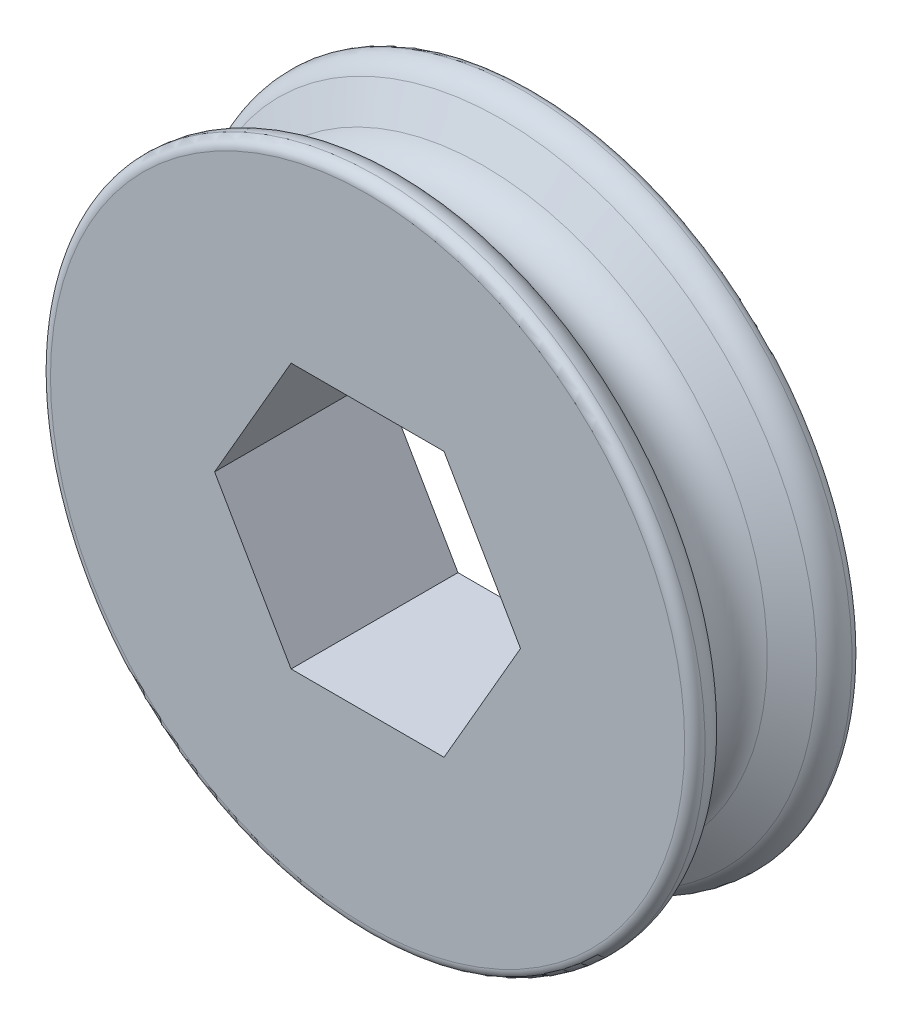
SolidWorks part; units mm, degrees
ref_plane "Front Plane" through (0, 0, 0) normal (0, 0, 1) x (1, 0, 0)
ref_plane "Top Plane" through (0, 0, 0) normal (0, 1, 0) x (1, 0, 0)
ref_plane "Right Plane" through (0, 0, 0) normal (1, 0, 0) x (0, 0, -1)
sketch "Sketch1" plane through (0, 0, 0) normal (1, 0, 0) x (0, 0, -1)
  line L0 (0, 0) -> (0, 17451.5356) construction
  line L1 (4, 0) -> (-4, 0)
  line L2 (-4, 0) -> (-4, 15.2006)
  line L3 (4, 0) -> (4, 15.2006)
  line L6 (-2.4257, 15.1015) -> (-1.5588, 13.6)
  line L7 (2.4257, 15.1015) -> (1.5588, 13.6)
  arc A0 (-4, 15.2006) -> (-3.525, 15.7) centre (-3.5, 15.2006) cw
  arc A1 (4, 15.2006) -> (3.525, 15.7) centre (3.5, 15.2006) ccw
  arc A2 (-3.525, 15.7) -> (-2.4257, 15.1015) centre (-3.465, 14.5015) cw
  arc A3 (3.525, 15.7) -> (2.4257, 15.1015) centre (3.465, 14.5015) ccw
  arc A4 (-1.5588, 13.6) -> (1.5588, 13.6) centre (0, 14.5) ccw
  point P6 (0, 0)
  point P18 (0, 12.7)
  dimension "D2" = 0.5
  dimension "D4" = 1.2
  dimension "D5" = 1.8
  dimension "D1" = 8
  dimension "D3" = 12.7
  dimension "D6" = 3
  dimension "D7" = 60
revolve "Revolve1" add sketch "Sketch1" angle 360 about L1
sketch "Sketch2" plane through (0, 0, 4) normal (0, 0, 1) x (1, 0, 0)
  line L1 (7.3323, 0) -> (3.6662, 6.35)
  line L2 (3.6662, 6.35) -> (-3.6662, 6.35)
  line L3 (-3.6662, 6.35) -> (-7.3323, 0)
  line L4 (-7.3323, 0) -> (-3.6662, -6.35)
  line L5 (-3.6662, -6.35) -> (3.6662, -6.35)
  line L6 (3.6662, -6.35) -> (7.3323, 0)
  circle A1 centre (0, 0) radius 15.2006
  circle A2 centre (0, 0) radius 15.2006
  circle A3 centre (0, 0) radius 6.35 construction
  dimension "D2" = 12.7
  dimension "D1" = 0
extrude "Cut-Extrude2" cut sketch "Sketch2" against normal through all contours L1 L2 L3 L4 L5 L6
